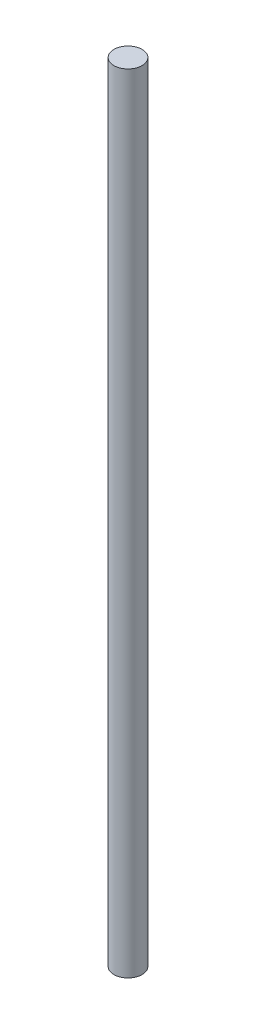
SolidWorks part; units mm, degrees
ref_plane "Front" through (0, 0, 0) normal (0, 0, 1) x (1, 0, 0)
ref_plane "Top" through (0, 0, 0) normal (0, 1, 0) x (1, 0, 0)
ref_plane "Right" through (0, 0, 0) normal (1, 0, 0) x (0, 0, -1)
sketch "Sketch1" plane through (0, 0, 0) normal (0, 1, 0) x (1, 0, 0)
  circle A0 centre (0, 0) radius 2.5
  dimension "D1" = 5
extrude "Boss-Extrude1" add sketch "Sketch1" along normal blind 140
equation "\"Kova_d\"= 155mm"
equation "\"Kova_h\"= 100mm"
equation "\"Plaka_h\"= 200mm"
equation "\"Plaka_L\"= 250mm"
equation "\"Saplama_d\"= 5mm"
equation "\"D1@Sketch1\"=\"Saplama_d\""
equation "\"Saplama_h\"= 140mm"
equation "\"D1@Boss-Extrude1\"=\"Saplama_h\""
